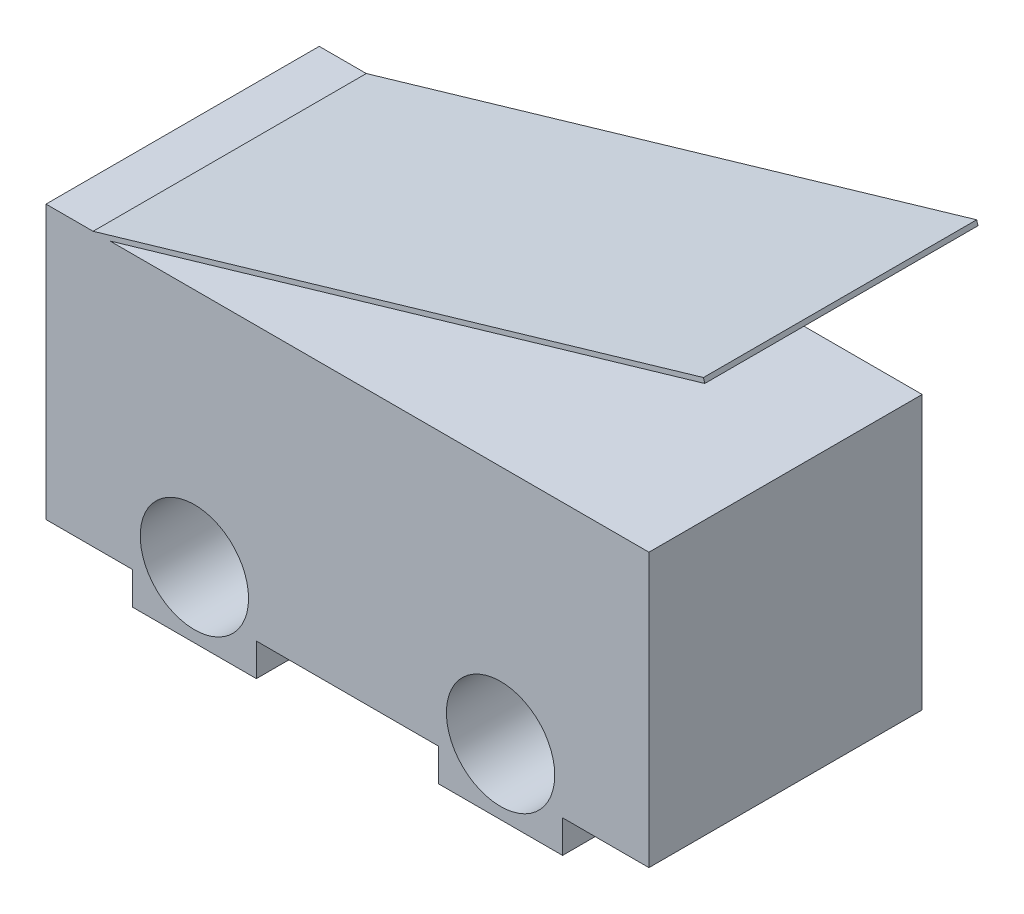
SolidWorks part; units mm, degrees
ref_plane "Front Plane" through (0, 0, 0) normal (0, 0, 1) x (1, 0, 0)
ref_plane "Top Plane" through (0, 0, 0) normal (0, 1, 0) x (1, 0, 0)
ref_plane "Right Plane" through (0, 0, 0) normal (1, 0, 0) x (0, 0, -1)
sketch "Sketch1" plane through (0, 0, 0) normal (0, 0, 1) x (1, 0, 0)
  line L0 (-6.4, -2.9) -> (-4.5658, -2.9)
  line L1 (6.4, -2.9) -> (-6.4, -2.9) construction
  line L2 (6.4, -2.9) -> (6.4, 2.9)
  line L3 (6.4, 2.9) -> (-6.4, 2.9)
  line L4 (-6.4, -2.9) -> (-6.4, 2.9)
  line L5 (6.4, -2.9) -> (-6.4, 2.9) construction
  line L6 (6.4, 2.9) -> (-6.4, -2.9) construction
  line L7 (-4.5658, -2.9) -> (-4.5658, -3.5923)
  line L8 (-4.5658, -3.5923) -> (-1.9342, -3.5923)
  line L9 (-1.9342, -3.5923) -> (-1.9342, -2.9)
  line L10 (-1.9342, -2.9) -> (1.9342, -2.9)
  line L11 (1.9342, -2.9) -> (1.9342, -3.5923)
  line L12 (1.9342, -3.5923) -> (4.5658, -3.5923)
  line L13 (4.5658, -3.5923) -> (4.5658, -2.9)
  line L14 (4.5658, -2.9) -> (6.4, -2.9)
  line L15 (0, 0) -> (0, -7.8977) construction
  circle A0 centre (-3.25, -2.2) radius 1.15
  circle A1 centre (3.25, -2.2) radius 1.15
  point P0 (0, 0)
  point P22 (-3.25, -3.5923)
  dimension "D5" = 2.3
  dimension "D1" = 5.8
  dimension "D2" = 12.8
  dimension "D3" = 6.5
  dimension "D4" = 5.1
  dimension "D6" = 0.6923
  dimension "D7" = 2.6317
extrude "Boss-Extrude1" add sketch "Sketch1" against normal blind 5.8
sketch "Sketch2" plane through (0, 0, 0) normal (0, 0, 1) x (1, 0, 0)
  line L0 (-6.4, 2.9) -> (-5.4, 2.9) construction
  line L1 (6.4, 2.9) -> (-6.4, 2.9) construction
  line L2 (-5.4, 2.9) -> (7.5571, 6.69)
  dimension "D1" = 1
  dimension "D2" = 13.5
  dimension "D3" = 9.59
extrude "Extrude-Thin1" add sketch "Sketch2" against normal up to surface (5.8 mm away) thin contours L2
